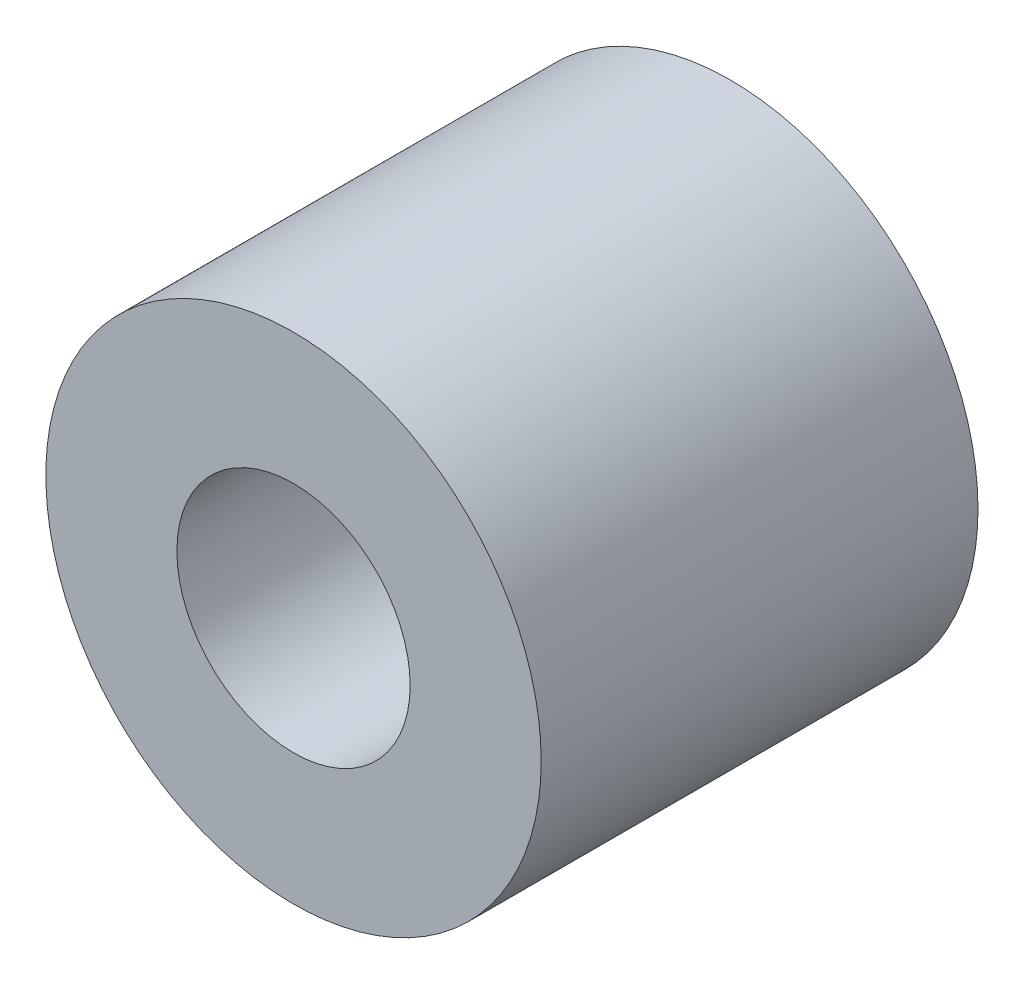
SolidWorks part; units mm, degrees
ref_plane "Front Plane" through (0, 0, 0) normal (0, 0, 1) x (1, 0, 0)
ref_plane "Top Plane" through (0, 0, 0) normal (0, 1, 0) x (1, 0, 0)
ref_plane "Right Plane" through (0, 0, 0) normal (1, 0, 0) x (0, 0, -1)
sketch "Sketch1" plane through (0, 0, 0) normal (0, 0, 1) x (1, 0, 0)
  circle A0 centre (0, 0) radius 1.335
  circle A1 centre (0, 0) radius 2.835
  dimension "D1" = 2.67
  dimension "D2" = 1.5
extrude "Boss-Extrude1" add sketch "Sketch1" along normal blind 5
